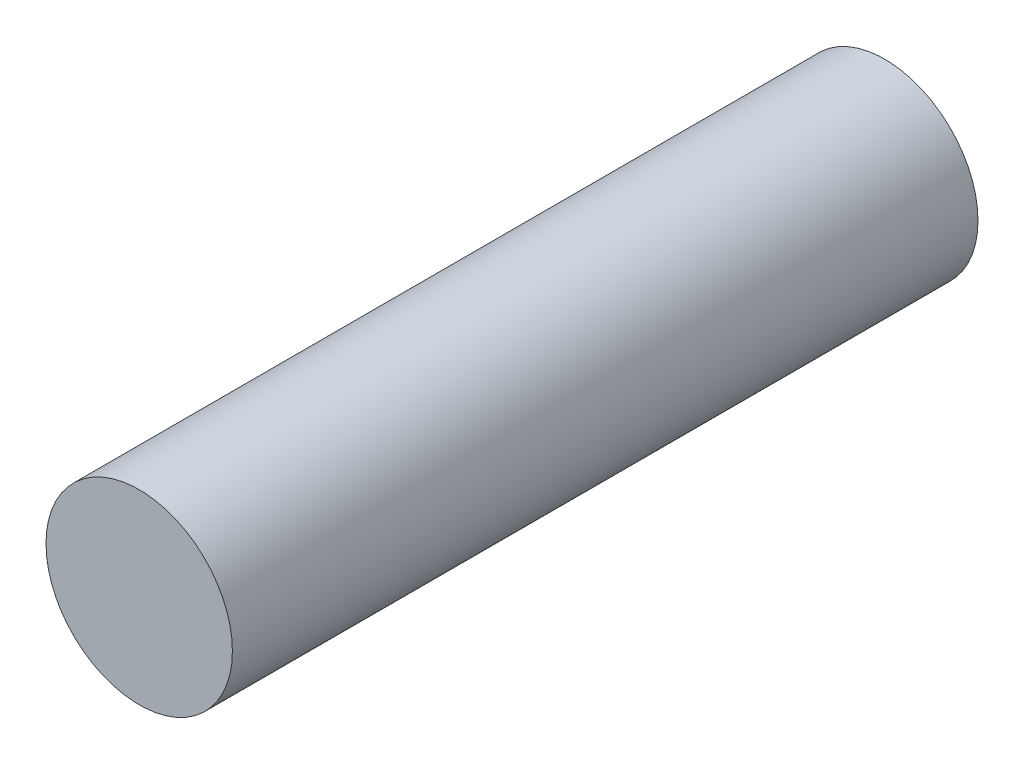
SolidWorks part; units mm, degrees
material "Brass"
ref_plane "Front Plane" through (0, 0, 0) normal (0, 0, 1) x (1, 0, 0)
ref_plane "Top Plane" through (0, 0, 0) normal (0, 1, 0) x (1, 0, 0)
ref_plane "Right Plane" through (0, 0, 0) normal (1, 0, 0) x (0, 0, -1)
sketch "Sketch1" plane through (0, 0, 0) normal (0, 0, 1) x (1, 0, 0)
  circle A0 centre (0, 0) radius 1.25
extrude "Boss-Extrude1" add sketch "Sketch1" along normal blind 10
